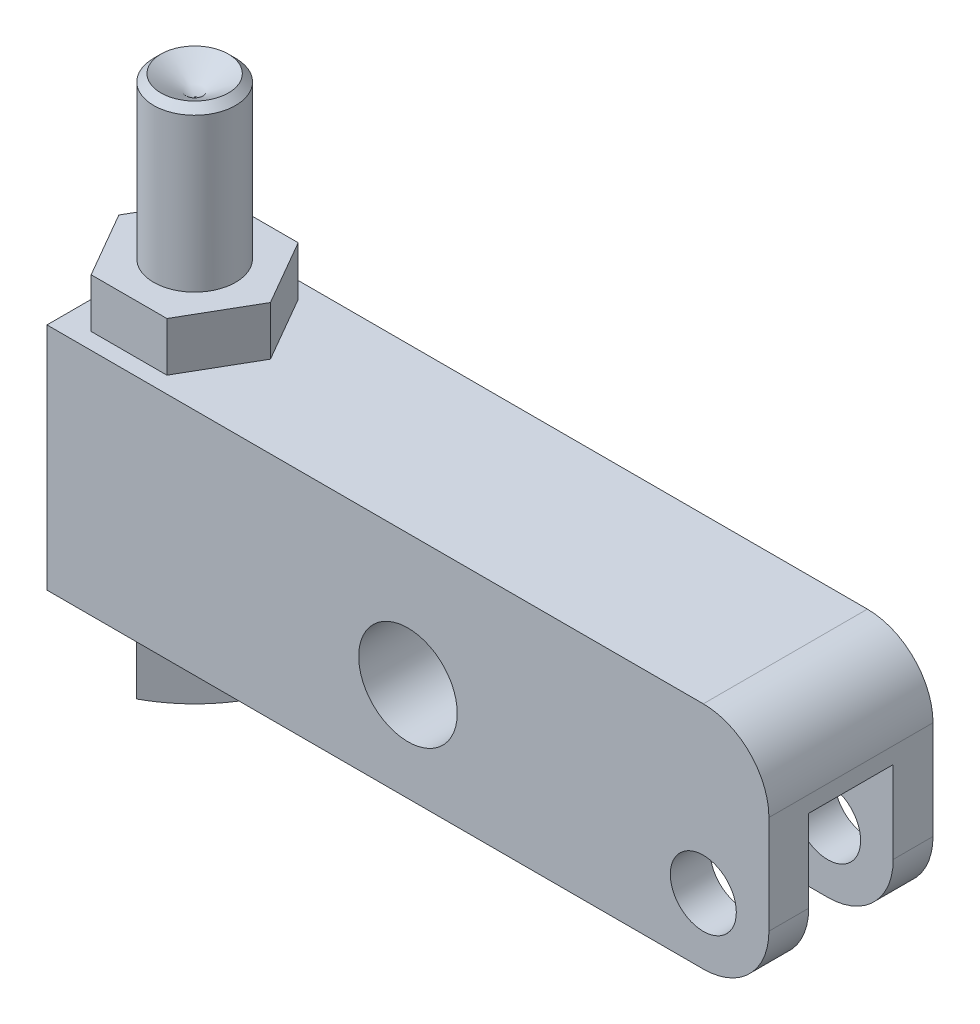
SolidWorks part; units mm, degrees
material "Alloy Steel"
ref_plane "Front Plane" through (0, 0, 0) normal (0, 0, 1) x (1, 0, 0)
ref_plane "Top Plane" through (0, 0, 0) normal (0, 1, 0) x (1, 0, 0)
ref_plane "Right Plane" through (0, 0, 0) normal (1, 0, 0) x (0, 0, -1)
sketch "Sketch11" plane through (0, 0, 0) normal (0, 0, 1) x (1, 0, 0)
  line L1 (-63.5, 15.875) -> (6.35, 15.875)
  line L2 (-63.5, 15.875) -> (-63.5, -6.35)
  line L3 (-63.5, -6.35) -> (6.35, -6.35)
  line L4 (6.35, 15.875) -> (6.35, -6.35)
  circle A0 centre (0, 0) radius 3.194
  circle A1 centre (-28.575, 3.175) radius 4.7689
  dimension "D1" = 6.3881
  dimension "D6" = 9.5377
  dimension "D2" = 6.35
  dimension "D3" = 63.5
  dimension "D4" = 22.225
  dimension "D5" = 28.575
  dimension "D7" = 6.35
  dimension "D8" = 3.175
extrude "Extrude3" add sketch "Sketch11" along normal mid plane 15.875
sketch "Sketch12" plane through (0, -6.35, 0) normal (0, -1, 0) x (1, 0, 0)
  line L0 (0, 0) -> (-16.2248, 0) construction
  line L1 (-7.9248, 4.0894) -> (6.35, 4.0894)
  line L2 (6.35, 7.9375) -> (6.35, -7.9375) construction
  line L3 (6.35, 4.0894) -> (6.35, -4.0894)
  line L4 (-63.5, 7.9375) -> (6.35, 7.9375) construction
  line L5 (-7.9248, -4.0894) -> (6.35, -4.0894)
  arc A0 (-7.9248, 4.0894) -> (-7.9248, -4.0894) centre (-7.9248, 0) ccw
  dimension "D3" = 18.3642
  dimension "D1" = 8.1788
  dimension "D2" = 3.8481
extrude "Cut-Extrude1" cut sketch "Sketch12" against normal blind 14.3002
fillet "Fillet1" radius 6.35 3 edges at (6.35, 15.875, 0) (6.35, -6.35, -6.0134) (6.35, -6.35, 6.0134)
sketch "Sketch13" plane through (0, 15.875, 0) normal (0, 1, 0) x (1, 0, 0)
  line L1 (-49.8177, 0) -> (-53.4838, 6.35)
  line L2 (-53.4838, 6.35) -> (-60.8162, 6.35)
  line L3 (-60.8162, 6.35) -> (-64.4823, 0)
  line L4 (-64.4823, 0) -> (-60.8162, -6.35)
  line L5 (-60.8162, -6.35) -> (-53.4838, -6.35)
  line L6 (-53.4838, -6.35) -> (-49.8177, 0)
  circle A0 centre (-57.15, 0) radius 6.35 construction
  dimension "D1" = 12.7
  dimension "D2" = 57.15
extrude "Extrude4" add sketch "Sketch13" along normal blind 4.7498
sketch "Sketch14" plane through (0, 0, 0) normal (0, 0, 1) x (1, 0, 0)
  line L0 (-57.15, 26.5852) -> (-57.15, -12.9942) construction
  line L1 (-49.8177, 20.6248) -> (-49.8177, 15.875) construction
  line L2 (-64.4823, 20.6248) -> (-64.4823, 15.875) construction
  line L3 (-57.15, 34.1831) -> (-60.4139, 36.1442)
  line L4 (-60.4139, 36.1442) -> (-61.1124, 35.4457)
  line L5 (-61.1124, 35.4457) -> (-61.1124, -8.3058)
  line L6 (-61.1124, -8.3058) -> (-70.5369, -8.3058)
  line L7 (-70.5369, -8.3058) -> (-70.5369, -9.0678)
  line L9 (-57.15, 34.1831) -> (-57.15, -14.2748)
  line L10 (-63.5, -6.35) -> (0, -6.35) construction
  arc A0 (-70.5369, -9.0678) -> (-57.15, -14.2748) centre (-57.15, 5.5372) ccw
  dimension "D5" = 19.812
  dimension "D1" = 59
  dimension "D2" = 6.5278
  dimension "D3" = 45
  dimension "D4" = 44.45
  dimension "D6" = 7.9248
  dimension "D7" = 5.969
  dimension "D8" = 0.762
  dimension "D9" = 7.9248
  dimension "D10" = 57.15
revolve "Revolve2" add sketch "Sketch14" angle 360 about L0
sketch "Sketch15" plane through (0, -8.3058, 0) normal (0, 1, 0) x (1, 0, 0)
  line L0 (-51.5463, 0) -> (-62.7537, 0) construction
  line L1 (-57.15, 5.6037) -> (-62.7537, 0)
  line L2 (-62.7537, 0) -> (-57.15, -5.6037)
  line L3 (-57.15, -5.6037) -> (-51.5463, 0)
  line L4 (-51.5463, 0) -> (-57.15, 5.6037)
  circle A0 centre (-57.15, 0) radius 3.9624 construction
  circle A1 centre (-57.15, 0) radius 13.3869 construction
  circle A2 centre (-57.15, 0) radius 13.3869
  dimension "D1" = 7.9248
extrude "Cut-Extrude2" cut sketch "Sketch15" against normal through all
